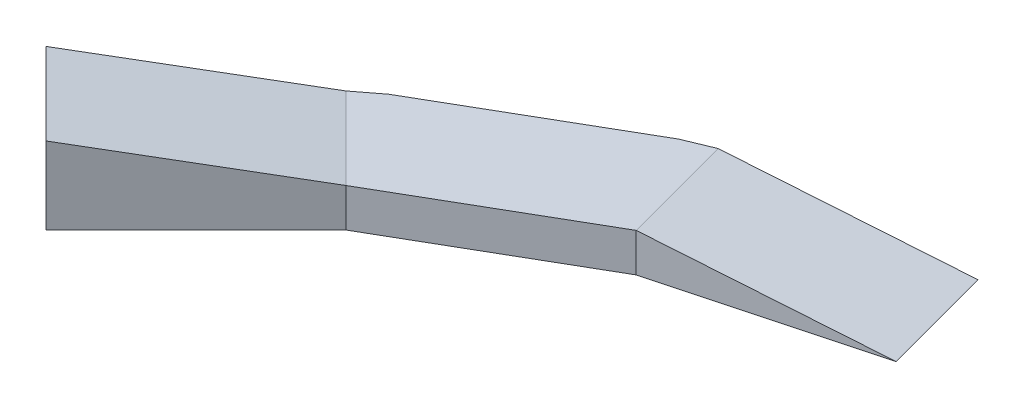
SolidWorks part; units mm, degrees
ref_plane "Front Plane" through (0, 0, 0) normal (0, 0, 1) x (1, 0, 0)
ref_plane "Top Plane" through (0, 0, 0) normal (0, 1, 0) x (1, 0, 0)
ref_plane "Right Plane" through (0, 0, 0) normal (1, 0, 0) x (0, 0, -1)
sketch "Sketch1" plane through (0, 0, 0) normal (0, 1, 0) x (1, 0, 0)
  line L0 (0, 0) -> (-1000, 0)
  line L1 (0, 0) -> (0, 600)
  line L2 (0, 600) -> (-1000, 600)
  line L3 (-1000, 0) -> (-2062.5184, -284.7009)
  line L4 (-2062.5184, -284.7009) -> (-3015.1464, -834.7009)
  line L5 (-1155.2914, 579.5555) -> (-2217.8098, 294.8545)
  line L6 (-1000, 600) -> (-1155.2914, 579.5555)
  line L7 (-3015.1464, -834.7009) -> (-3792.9638, -1612.5184)
  line L8 (-2217.8098, 294.8545) -> (-2362.5184, 234.9143)
  line L9 (-2362.5184, 234.9143) -> (-3315.1464, -315.0857)
  line L10 (-4217.2279, -1188.2543) -> (-3792.9638, -1612.5184)
  line L11 (-3439.4104, -410.4369) -> (-4217.2279, -1188.2543)
  line L12 (-3315.1464, -315.0857) -> (-3439.4104, -410.4369)
extrude "Boss-Extrude1" add sketch "Sketch1" against normal blind 600
sketch "Sketch24" plane through (0, 0, 0) normal (0, 1, 0) x (1, 0, 0)
  line L0 (-1000, 0) -> (-1155.2914, 579.5555)
  line L1 (-1155.2914, 579.5555) -> (-1000, 600)
  line L2 (-1000, 600) -> (0, 600)
  line L3 (0, 600) -> (0, 0)
  line L4 (0, 0) -> (-1000, 0)
extrude "Cut-Extrude1" cut sketch "Sketch24" against normal blind 600
sketch "Sketch25" plane through (-66.9873, 0, -250) normal (0.2588, 0, 0.9659) x (0.9659, 0, -0.2588)
  line L0 (-965.9258, -600) -> (-2065.9258, -600)
  line L1 (-2065.9258, 0) -> (-2065.9258, -400)
  line L2 (-2065.9258, -600) -> (-2065.9258, 0) construction
  line L3 (-965.9258, -600) -> (-2065.9258, -400)
  line L4 (-2065.9258, -400) -> (-2065.9258, 0)
  line L5 (-2065.9258, 0) -> (-965.9258, 0)
  line L6 (-965.9258, 0) -> (-965.9258, -600)
  line M1 (-965.9258, 0) -> (-2065.9258, 0)
  line M2 (-2065.9258, 0) -> (-2065.9258, -600)
  line M4 (-965.9258, -600) -> (-965.9258, 0)
extrude "Cut-Extrude2" cut sketch "Sketch25" against normal blind 600 contours L3 M4 M1 M2
sketch "Sketch26" plane through (-392.3505, 0, -679.571) normal (0.5, 0, 0.866) x (0.866, 0, -0.5)
  line L0 (-1928.5438, -400) -> (-3028.5438, -400)
  line L1 (-3028.5438, -600) -> (-3028.5438, 0) construction
  line L2 (-3028.5438, -400) -> (-3028.5438, 0)
  line L3 (-3028.5438, 0) -> (-1928.5438, 0)
  line L4 (-1928.5438, 0) -> (-1928.5438, -400)
extrude "Cut-Extrude3" cut sketch "Sketch26" against normal blind 600
sketch "Sketch27" plane through (-429.0376, 0, -1035.7883) normal (-0.3827, 0, -0.9239) x (-0.9239, 0, 0.3827)
  line L0 (1936.1532, -400) -> (2092.7846, -400)
  line L1 (2092.7846, -400) -> (2092.7846, 0)
  line L2 (2092.7846, 0) -> (1936.1532, 0)
  line L3 (1936.1532, 0) -> (1936.1532, -400)
extrude "Cut-Extrude4" cut sketch "Sketch27" against normal blind 600
sketch "Sketch28" plane through (-1090.2227, 0, -1090.2227) normal (0.7071, 0, 0.7071) x (0.7071, 0, -0.7071)
  line L0 (-2722.2531, -400) -> (-3822.2531, -400)
  line L1 (-3822.2531, -600) -> (-3822.2531, 0) construction
  line L2 (-3822.2531, -400) -> (-3822.2531, -200)
sketch "Sketch30" plane through (0, 0, 0) normal (0, 1, 0) x (1, 0, 0)
  line L0 (-3439.4104, -410.4369) -> (-3015.1464, -834.7009)
  line L1 (-3015.1464, -834.7009) -> (-3315.1464, -315.0857)
  line L2 (-3315.1464, -315.0857) -> (-3439.4104, -410.4369)
extrude "Cut-Extrude6" cut sketch "Sketch30" against normal blind 400
sketch "Sketch31" plane through (-1090.2227, 0, -1090.2227) normal (0.7071, 0, 0.7071) x (0.7071, 0, -0.7071)
  line L0 (-2722.2531, -400) -> (-3822.2531, -200)
  line L1 (-3822.2531, -200) -> (-3822.2531, 0)
  line L2 (-3822.2531, 0) -> (-2722.2531, 0)
  line L3 (-2722.2531, 0) -> (-2722.2531, -400)
extrude "Cut-Extrude7" cut sketch "Sketch31" against normal blind 600
